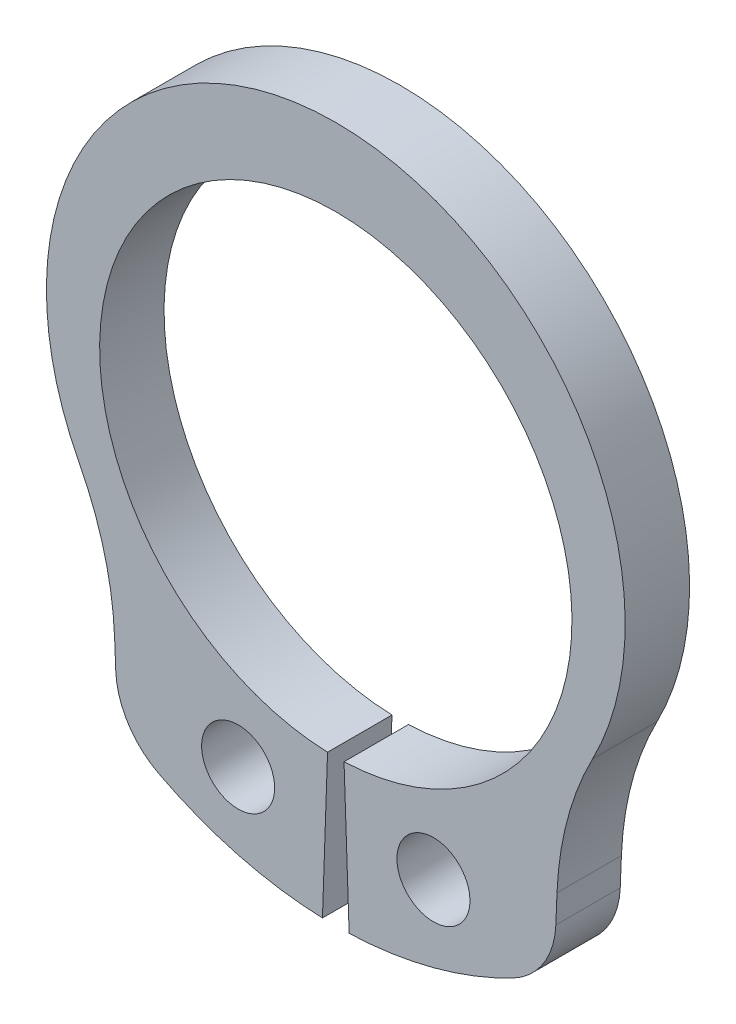
SolidWorks part; units mm, degrees
ref_plane "Front" through (0, 0, 0) normal (0, 0, 1) x (1, 0, 0)
ref_plane "Top" through (0, 0, 0) normal (0, 1, 0) x (1, 0, 0)
ref_plane "Right" through (0, 0, 0) normal (1, 0, 0) x (0, 0, -1)
sketch "Sketch1" plane through (0, 0, 0) normal (0, 0, 1) x (1, 0, 0)
  line L0 (0, 0) -> (-4.7631, -2.75) construction
  line L1 (0, 8.9) -> (0, -8.9) construction
  line L2 (-5.084, -7.3116) -> (-5.2314, -3.6867) construction
  line L4 (-5.2314, -3.6867) -> (-5.9671, -4.2052) construction
  line L5 (-5.2314, -3.6867) -> (0, 0) construction
  line L6 (0, 5.5) -> (0, 7.3) construction
  line L7 (0, 7.3) -> (0, 6.4) construction
  line L8 (0, -5.5) -> (0, -8.9) construction
  line L9 (-2.8119, -8.4498) -> (0, 0) construction
  line L10 (0, 0) -> (-0.3108, -8.9) construction
  line L11 (-5.084, -7.3116) -> (0, 0) construction
  line L12 (-5.1777, -5.0091) -> (-5.9608, -2.5823) construction
  line L13 (-5.5692, -3.7957) -> (-5.2314, -3.6867) construction
  line L14 (-1.7366, -5.2186) -> (-2.8119, -8.4498) construction
  line L15 (-2.2743, -6.8342) -> (-1.4678, -7.1026) construction
  arc A0 (0, 7.3) -> (-5.2314, -3.6867) centre (0, 0.5611) ccw construction
  circle A2 centre (0, 0) radius 7.3 construction
  arc A3 (-5.084, -7.3116) -> (-0.3108, -8.9) centre (0, 0) ccw construction
  circle A4 centre (0, 0) radius 5.5 construction
  circle A6 centre (-2.2743, -6.8342) radius 0.85 construction
  arc A7 (-5.9608, -2.5823) -> (-5.1777, -5.0091) centre (-12.5069, -6.0345) cw construction
  point P5 (-4.7631, -2.75)
  point P24 (-4.1675, -5.9935)
  point P35 (0, 7.3)
  point P36 (0, 5.5)
  point P37 (0, -5.5)
  point P38 (0, -8.9)
  dimension "Ring ID" = 11
  dimension "Hole Diameter" = 1.7
  dimension "D10" = 7.4006
  dimension "Max Sec." = 1.8
  dimension "Lug Height" = 3.4
  dimension "D6" = 2
  dimension "D5" = 3.6278
  dimension "D8" = 2.55
  dimension "D3" = 120
  dimension "D2" = 5.1
  dimension "D4" = 2.55
sketch "Sketch5" plane through (0, 0, 0) normal (0, 1, 0) x (1, 0, 0)
  line L0 (-7.3, 0.75) -> (-7.3, -0.75) construction
  line L2 (0, 0.75) -> (0, -0.75) construction
  line L4 (-7.3, 0) -> (7.3, 0) construction
  point P3 (-7.3, 0)
  point P6 (0, 0)
  dimension "Ring Thickness" = 1.5
sketch "Sketch2" plane through (0, 0, 0) normal (0, 0, 1) x (1, 0, 0)
  line L0 (-5.084, -7.3116) -> (-5.2314, -3.6867) construction
  line L1 (-5.084, -7.3116) -> (-5.2314, -3.6867)
  line L2 (0, 7.3) -> (0, 5.5)
  line L3 (-0.3108, -8.9) -> (-0.1919, -5.4966)
  line L4 (0, 0) -> (-0.3108, -8.9) construction
  arc A0 (0, 7.3) -> (-5.2314, -3.6867) centre (0, 0.5611) ccw construction
  arc A1 (-5.084, -7.3116) -> (-0.3108, -8.9) centre (0, 0) ccw construction
  circle A2 centre (-2.2743, -6.8342) radius 0.85 construction
  arc A4 (0, 7.3) -> (-5.2314, -3.6867) centre (0, 0.5611) ccw
  arc A5 (-5.084, -7.3116) -> (-0.3108, -8.9) centre (0, 0) ccw
  circle A6 centre (-2.2743, -6.8342) radius 0.85
  circle A7 centre (0, 0) radius 5.5 construction
  arc A8 (0, 5.5) -> (-0.1919, -5.4966) centre (0, 0) ccw
extrude "Boss-Extrude1" add sketch "Sketch2" along normal mid plane 1.5
fillet "Fillet1" radius 7.4006 1 edges at (-5.2314, -3.6867, 0)
fillet "Fillet2" radius 1.8502 1 edges at (-5.084, -7.3116, 0)
mirror "Mirror1" about plane through (0, 7.3, 0.75) normal (-1, 0, 0) of bodies 109
sketch "Sketch3" plane through (0, 0, 0.75) normal (0, 0, 1) x (1, 0, 0)
  line L0 (5.0897, -2.0846) -> (5.9793, -2.547) construction
  line L1 (5.9793, -2.547) -> (6.4417, -1.6574) construction
  line L2 (0, 7.3) -> (0, 5.5) construction
  circle A0 centre (0, 0) radius 5.5 construction
  arc A1 (5.9793, -2.547) -> (-5.9793, -2.547) centre (0, 0.5611) ccw construction
equation "\"D1@Fillet1\" = \"D10@Sketch1\""
equation "\"D1@Fillet2\" = \"D10@Sketch1\" / 4"
equation "\"Thickness@Boss-Extrude1\"=\"Ring Thickness@Sketch5\""
equation "\"D2@Sketch1\"=\"Hole Diameter@Sketch1\"*3"
equation "\"D4@Sketch1\"=\"D2@Sketch1\"/2"
equation "\"D8@Sketch1\"=\"D4@Sketch1\""
